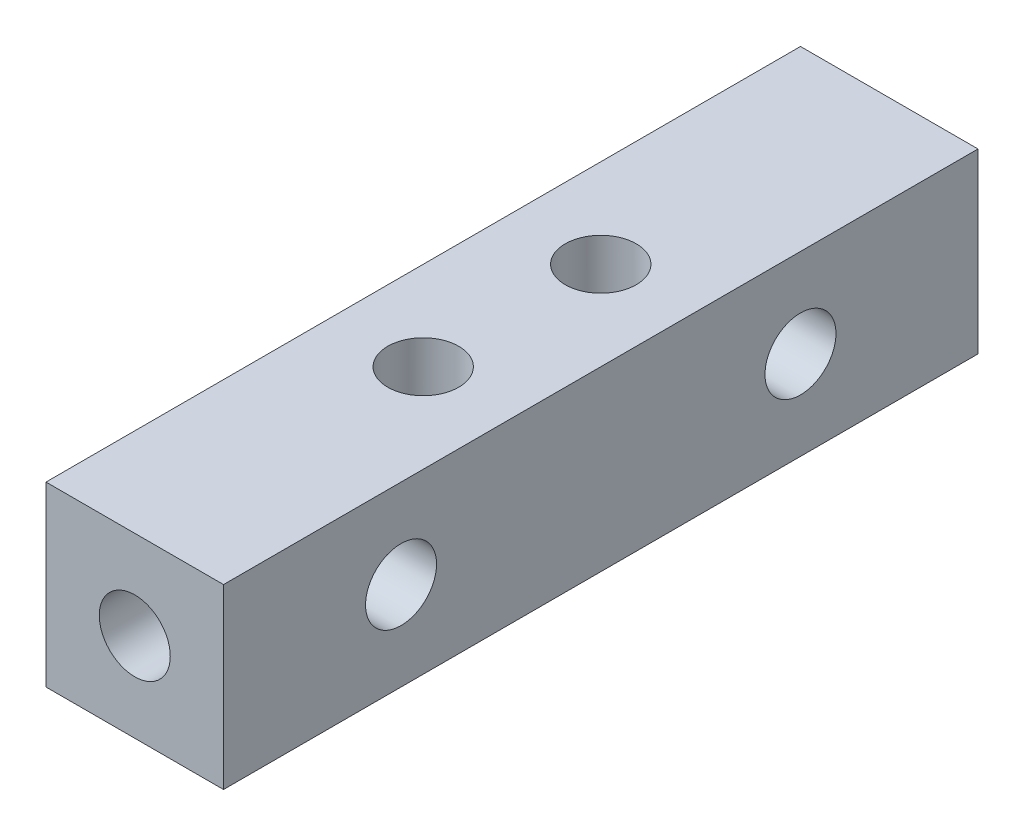
SolidWorks part; units mm, degrees
material "6061 合金"
ref_plane "前视基准面" through (0, 0, 0) normal (0, 0, 1) x (1, 0, 0)
ref_plane "上视基准面" through (0, 0, 0) normal (0, 1, 0) x (1, 0, 0)
ref_plane "右视基准面" through (0, 0, 0) normal (1, 0, 0) x (0, 0, -1)
sketch "草图1" plane through (0, 0, 0) normal (0, 0, 1) x (1, 0, 0)
  line L1 (1.8325, 2.3053) -> (9.8325, 2.3053)
  line L2 (1.8325, 2.3053) -> (1.8325, 10.3053)
  line L3 (1.8325, 10.3053) -> (9.8325, 10.3053)
  line L4 (9.8325, 2.3053) -> (9.8325, 10.3053)
  dimension "D1" = 8
  dimension "D2" = 8
extrude "凸台-拉伸1" add sketch "草图1" along normal blind 34
sketch "草图2" plane through (0, 0, 34) normal (0, 0, 1) x (1, 0, 0)
  line L0 (9.8325, 2.3053) -> (9.8325, 10.3053) construction
  line L1 (9.8325, 10.3053) -> (1.8325, 10.3053) construction
  circle A0 centre (5.8325, 6.3053) radius 1.6
  dimension "D1" = 3.2
  dimension "D3" = 4
  dimension "D2" = 4
extrude "切除-拉伸1" cut sketch "草图2" against normal through all
sketch "草图3" plane through (0, 10.3053, 0) normal (0, 1, 0) x (1, 0, 0)
  line L0 (9.8325, -34) -> (9.8325, 0) construction
  line L1 (9.8325, -34) -> (1.8325, -34) construction
  circle A0 centre (5.8325, -13) radius 1.6
  circle A1 centre (5.8325, -21) radius 1.6
  dimension "D1" = 8
  dimension "D2" = 3.2
  dimension "D3" = 3.2
  dimension "D4" = 4
  dimension "D5" = 13
extrude "切除-拉伸2" cut sketch "草图3" against normal blind 34
sketch "草图4" plane through (9.8325, 0, 0) normal (1, 0, 0) x (0, 0, -1)
  line L0 (0, 2.3053) -> (0, 10.3053) construction
  line L1 (-34, 10.3053) -> (0, 10.3053) construction
  circle A0 centre (-26, 6.3053) radius 1.6
  circle A1 centre (-8, 6.3053) radius 1.6
  dimension "D1" = 3.2
  dimension "D2" = 3.2
  dimension "D3" = 18
  dimension "D4" = 8
  dimension "D5" = 4
  dimension "D6" = 4
extrude "切除-拉伸3" cut sketch "草图4" against normal blind 34
